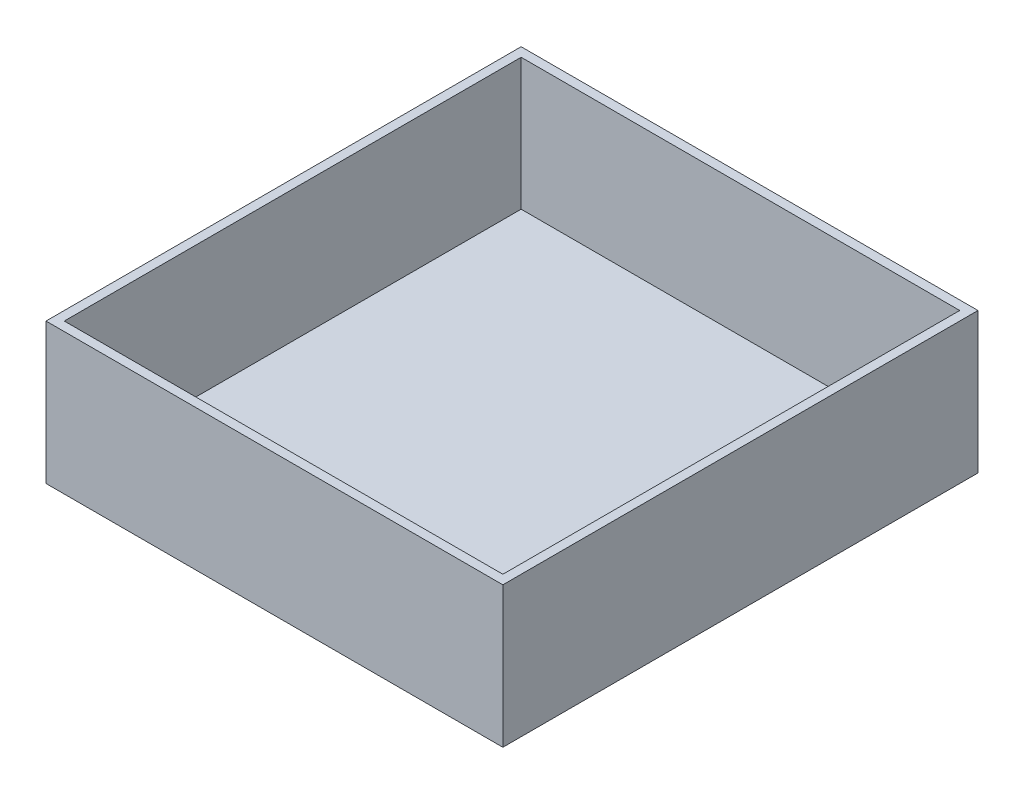
SolidWorks part; units mm, degrees
ref_plane "Front Plane" through (0, 0, 0) normal (0, 0, 1) x (1, 0, 0)
ref_plane "Top Plane" through (0, 0, 0) normal (0, 1, 0) x (1, 0, 0)
ref_plane "Right Plane" through (0, 0, 0) normal (1, 0, 0) x (0, 0, -1)
sketch "Sketch1" plane through (0, 0, 0) normal (0, 1, 0) x (1, 0, 0)
  line L1 (-79.375, -82.55) -> (79.375, -82.55)
  line L2 (-79.375, -82.55) -> (-79.375, 82.55)
  line L3 (-79.375, 82.55) -> (79.375, 82.55)
  line L4 (79.375, -82.55) -> (79.375, 82.55)
  line L5 (-79.375, -82.55) -> (79.375, 82.55) construction
  line L6 (-79.375, 82.55) -> (79.375, -82.55) construction
  point P0 (0, 0)
  dimension "D1" = 165.1
  dimension "D2" = 158.75
extrude "Boss-Extrude1" add sketch "Sketch1" along normal blind 3.175
sketch "Sketch2" plane through (0, 3.175, 0) normal (0, 1, 0) x (1, 0, 0)
  line L8 (76.2, -79.375) -> (76.2, 79.375)
  line L9 (76.2, 79.375) -> (-76.2, 79.375)
  line L10 (-76.2, 79.375) -> (-76.2, -79.375)
  line L11 (-76.2, -79.375) -> (76.2, -79.375)
  line L12 (76.2, -79.375) -> (76.2, 79.375)
  line L13 (76.2, 79.375) -> (-76.2, 79.375)
  line L14 (-76.2, 79.375) -> (-76.2, -79.375)
  line L15 (-76.2, -79.375) -> (76.2, -79.375)
  line L16 (79.375, -82.55) -> (79.375, 82.55)
  line L17 (79.375, 82.55) -> (-79.375, 82.55)
  line L18 (-79.375, 82.55) -> (-79.375, -82.55)
  line L19 (-79.375, -82.55) -> (79.375, -82.55)
  line L20 (79.375, -82.55) -> (79.375, 82.55)
  line L21 (79.375, 82.55) -> (-79.375, 82.55)
  line L22 (-79.375, 82.55) -> (-79.375, -82.55)
  line L23 (-79.375, -82.55) -> (79.375, -82.55)
  dimension "D1" = 3.175
  dimension "D2" = 0
extrude "Boss-Extrude2" add sketch "Sketch2" along normal blind 45.72
